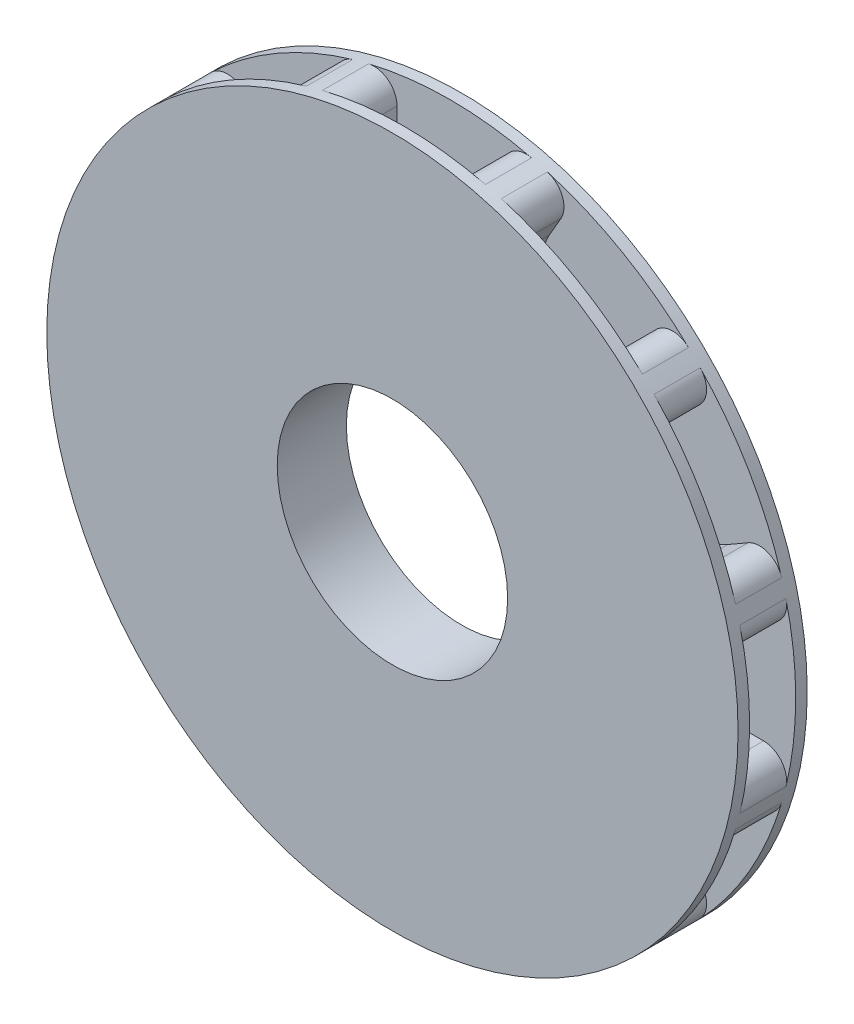
SolidWorks part; units mm, degrees
ref_plane "Front" through (0, 0, 0) normal (0, 0, 1) x (1, 0, 0)
ref_plane "Top" through (0, 0, 0) normal (0, 1, 0) x (1, 0, 0)
ref_plane "Right" through (0, 0, 0) normal (1, 0, 0) x (0, 0, -1)
sketch "Sketch1" plane through (0, 0, 0) normal (0, 0, 1) x (1, 0, 0)
  circle A0 centre (0, 0) radius 7.5
  circle A1 centre (0, 0) radius 2.5
  dimension "D1" = 15
  dimension "D2" = 5
extrude "Boss-Extrude1" add sketch "Sketch1" along normal blind 1.5
ref_plane "Plane1" through (0, 0, 1.5) normal (0, 0, 1) x (1, 0, 0)
ref_plane "Plane2" through (0, 0, 0.75) normal (0, 0, 1) x (1, 0, 0)
sketch "Sketch2" plane through (0, 0, 0.75) normal (0, 0, 1) x (1, 0, 0)
  line L0 (1.15, 6.295) -> (1.15, 7.645)
  line L1 (-1.15, 6.295) -> (-1.15, 7.645)
  line L2 (0, 0) -> (0, 3.9622) construction
  line L3 (-1.15, 7.645) -> (1.15, 7.645)
  line L4 (2.1515, 6.0266) -> (2.8265, 7.1957)
  line L5 (4.1434, 4.8766) -> (4.8184, 6.0457)
  line L6 (4.8766, 4.1434) -> (6.0457, 4.8184)
  line L7 (6.0266, 2.1515) -> (7.1957, 2.8265)
  line L8 (6.295, 1.15) -> (7.645, 1.15)
  line L9 (6.295, -1.15) -> (7.645, -1.15)
  line L10 (6.0266, -2.1515) -> (7.1957, -2.8265)
  line L11 (4.8766, -4.1434) -> (6.0457, -4.8184)
  line L12 (4.1434, -4.8766) -> (4.8184, -6.0457)
  line L13 (2.1515, -6.0266) -> (2.8265, -7.1957)
  line L14 (1.15, -6.295) -> (1.15, -7.645)
  line L15 (-1.15, -6.295) -> (-1.15, -7.645)
  line L16 (-2.1515, -6.0266) -> (-2.8265, -7.1957)
  line L17 (-4.1434, -4.8766) -> (-4.8184, -6.0457)
  line L18 (-4.8766, -4.1434) -> (-6.0457, -4.8184)
  line L19 (-6.0266, -2.1515) -> (-7.1957, -2.8265)
  line L20 (-6.295, -1.15) -> (-7.645, -1.15)
  line L21 (-6.295, 1.15) -> (-7.645, 1.15)
  line L22 (-6.0266, 2.1515) -> (-7.1957, 2.8265)
  line L23 (-4.8766, 4.1434) -> (-6.0457, 4.8184)
  line L24 (-4.1434, 4.8766) -> (-4.8184, 6.0457)
  line L25 (-2.1515, 6.0266) -> (-2.8265, 7.1957)
  line L26 (2.8265, 7.1957) -> (4.8184, 6.0457)
  line L27 (6.0457, 4.8184) -> (7.1957, 2.8265)
  line L28 (7.645, 1.15) -> (7.645, -1.15)
  line L29 (7.1957, -2.8265) -> (6.0457, -4.8184)
  line L30 (4.8184, -6.0457) -> (2.8265, -7.1957)
  line L31 (1.15, -7.645) -> (-1.15, -7.645)
  line L32 (-2.8265, -7.1957) -> (-4.8184, -6.0457)
  line L33 (-6.0457, -4.8184) -> (-7.1957, -2.8265)
  line L34 (-7.645, -1.15) -> (-7.645, 1.15)
  line L35 (-7.1957, 2.8265) -> (-6.0457, 4.8184)
  line L36 (-4.8184, 6.0457) -> (-2.8265, 7.1957)
  arc A0 (-1.15, 6.295) -> (1.15, 6.295) centre (0, 6.295) ccw
  arc A1 (2.1515, 6.0266) -> (4.1434, 4.8766) centre (3.1475, 5.4516) ccw
  arc A2 (4.8766, 4.1434) -> (6.0266, 2.1515) centre (5.4516, 3.1475) ccw
  arc A3 (6.295, 1.15) -> (6.295, -1.15) centre (6.295, 0) ccw
  arc A4 (6.0266, -2.1515) -> (4.8766, -4.1434) centre (5.4516, -3.1475) ccw
  arc A5 (4.1434, -4.8766) -> (2.1515, -6.0266) centre (3.1475, -5.4516) ccw
  arc A6 (1.15, -6.295) -> (-1.15, -6.295) centre (0, -6.295) ccw
  arc A7 (-2.1515, -6.0266) -> (-4.1434, -4.8766) centre (-3.1475, -5.4516) ccw
  arc A8 (-4.8766, -4.1434) -> (-6.0266, -2.1515) centre (-5.4516, -3.1475) ccw
  arc A9 (-6.295, -1.15) -> (-6.295, 1.15) centre (-6.295, 0) ccw
  arc A10 (-6.0266, 2.1515) -> (-4.8766, 4.1434) centre (-5.4516, 3.1475) ccw
  arc A11 (-4.1434, 4.8766) -> (-2.1515, 6.0266) centre (-3.1475, 5.4516) ccw
  point P1 (0, 7.645)
  point P67 (0, 0)
  point P90 (0, 0)
  dimension "D1" = 1.35
  dimension "D2" = 12
  dimension "D3" = 12
extrude "Cut-Extrude1" cut sketch "Sketch2" against normal blind 0.5 and the other way blind 0.5
fillet "Fillet1" radius 0.5 24 edges at (-2.7097, 6.9934, 0.75) (-1.15, 7.4113, 0.75) (1.15, 7.4113, 0.75) (2.7097, 6.9934, 0.75) (4.7016, 5.8434, 0.75) (5.8434, 4.7016, 0.75) (6.9934, 2.7097, 0.75) (7.4113, 1.15, 0.75) (7.4113, -1.15, 0.75) (6.9934, -2.7097, 0.75) (5.8434, -4.7016, 0.75) (4.7016, -5.8434, 0.75) (2.7097, -6.9934, 0.75) (1.15, -7.4113, 0.75) (-1.15, -7.4113, 0.75) (-2.7097, -6.9934, 0.75) (-4.7016, -5.8434, 0.75) (-5.8434, -4.7016, 0.75) (-6.9934, -2.7097, 0.75) (-7.4113, -1.15, 0.75) (-7.4113, 1.15, 0.75) (-6.9934, 2.7097, 0.75) (-5.8434, 4.7016, 0.75) (-4.7016, 5.8434, 0.75)
